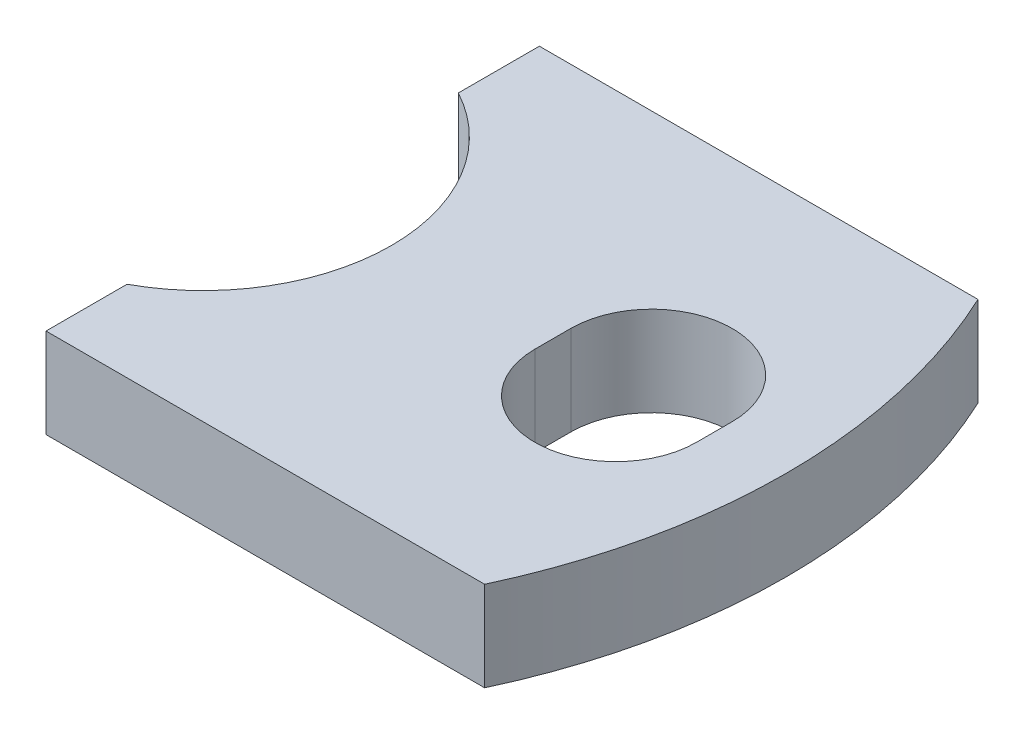
SolidWorks part; units mm, degrees
ref_plane "Front Plane" through (0, 0, 0) normal (0, 0, 1) x (1, 0, 0)
ref_plane "Top Plane" through (0, 0, 0) normal (0, 1, 0) x (1, 0, 0)
ref_plane "Right Plane" through (0, 0, 0) normal (1, 0, 0) x (0, 0, -1)
sketch "Sketch2" plane through (0, 0, 0) normal (0, 1, 0) x (1, 0, 0)
  line L1 (-2.75, -2.75) -> (2.75, -2.75)
  line L2 (-2.75, -2.75) -> (-2.75, 2.75)
  line L3 (-2.75, 2.75) -> (2.75, 2.75)
  line L4 (2.75, -2.75) -> (2.75, 2.75)
  line L5 (-2.75, -2.75) -> (2.75, 2.75) construction
  line L6 (-2.75, 2.75) -> (2.75, -2.75) construction
  point P0 (0, 0)
  dimension "D1" = 5.5
  dimension "D2" = 5.5
extrude "Boss-Extrude1" add sketch "Sketch2" along normal blind 1
sketch "Sketch3" plane through (0, 1, 0) normal (0, 1, 0) x (1, 0, 0)
  line L2 (-2.75, 0) -> (2.75, 0) construction
  line L4 (-2.75, 2.75) -> (-2.75, -2.75) construction
  line L6 (2.75, -2.75) -> (2.75, 2.75) construction
  line L7 (1.05, -0.2) -> (1.05, 0.2) construction
  line L8 (0.15, -0.2) -> (0.15, 0.2)
  line L9 (1.95, -0.2) -> (1.95, 0.2)
  arc A0 (0.15, -0.2) -> (1.95, -0.2) centre (1.05, -0.2) ccw
  arc A1 (1.95, 0.2) -> (0.15, 0.2) centre (1.05, 0.2) ccw
  point P8 (1.05, 0)
  dimension "D1" = 2.2
  dimension "D2" = 1.8
  dimension "D3" = 3.8
extrude "Cut-Extrude1" cut sketch "Sketch3" against normal through all
sketch "Sketch4" plane through (0, 1, 0) normal (0, 1, 0) x (1, 0, 0)
  line L0 (-2.75, 2.75) -> (-2.75, -2.75) construction
  line L1 (-2.75, 1.8466) -> (-2.75, -1.8466)
  arc A0 (-2.75, -1.8466) -> (-2.75, 1.8466) centre (-3.75, 0) ccw
  arc A3 (1.95, 0.2) -> (0.15, 0.2) centre (1.05, 0.2) ccw construction
  point P1 (1.05, 1.1)
  dimension "D1" = 2.7
  dimension "D2" = 2.1
extrude "Cut-Extrude2" cut sketch "Sketch4" against normal through all
sketch "Sketch5" plane through (0, 1, 0) normal (0, 1, 0) x (1, 0, 0)
  line L1 (2.75, 2.75) -> (-2.75, 2.75) construction
  line L2 (3.85, -2.75) -> (3.85, 2.75)
  line L3 (3.85, -2.75) -> (3.85, 2.75)
  line L4 (3.85, 2.75) -> (2.1396, 2.75)
  line L5 (-2.75, -2.75) -> (2.75, -2.75) construction
  line L6 (2.1396, -2.75) -> (3.85, -2.75)
  arc A0 (2.1396, -2.75) -> (2.1396, 2.75) centre (-3.75, 0) ccw
  dimension "D2" = 6.5
  dimension "D1" = 1.1
extrude "Cut-Extrude3" cut sketch "Sketch5" against normal blind 1
